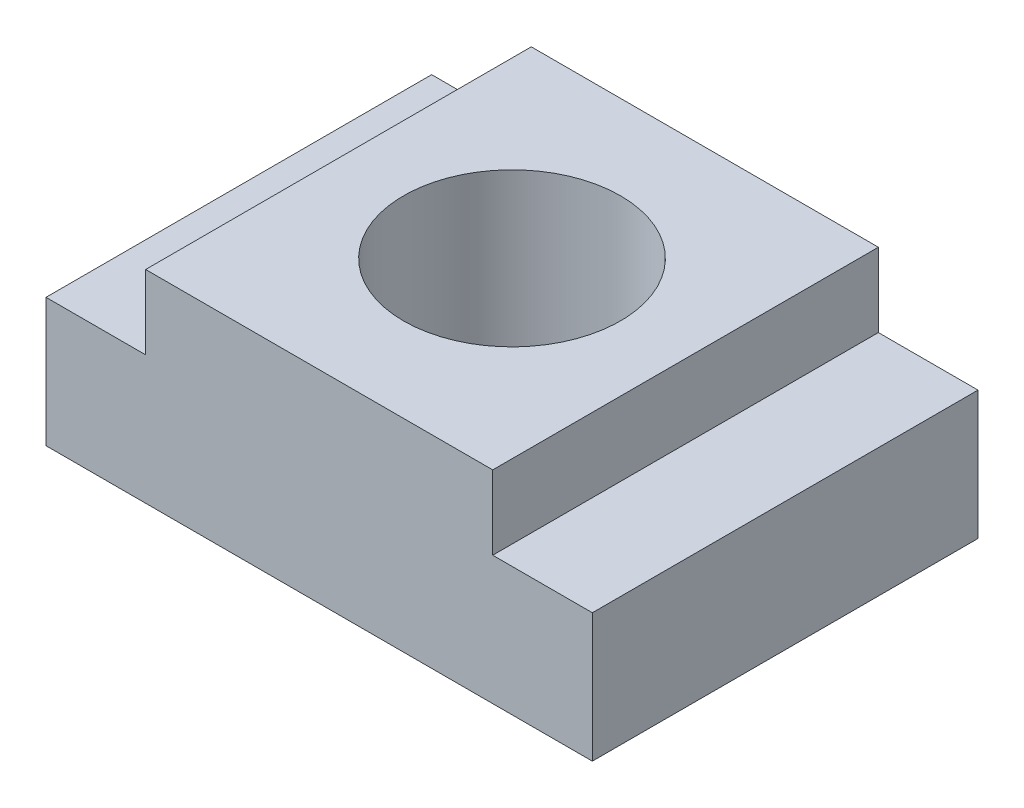
SolidWorks part; units mm, degrees
material "Chrome Stainless Steel"
ref_plane "Front Plane" through (0, 0, 0) normal (0, 0, 1) x (1, 0, 0)
ref_plane "Top Plane" through (0, 0, 0) normal (0, 1, 0) x (1, 0, 0)
ref_plane "Right Plane" through (0, 0, 0) normal (1, 0, 0) x (0, 0, -1)
sketch "Sketch1" plane through (0, 0, 0) normal (0, 0, 1) x (1, 0, 0)
  line L0 (0, 6.3) -> (5.4, 6.3)
  line L1 (0, -55) -> (0, 55) construction
  line L2 (5.4, 6.3) -> (5.4, 4)
  line L3 (5.4, 4) -> (8.5, 4)
  line L4 (8.5, 4) -> (8.5, 0)
  line L5 (55, 0) -> (-55, 0) construction
  line L6 (8.5, 0) -> (0, 0)
  line L7 (0, 0) -> (0, 6.3)
  dimension "D1" = 5.4
  dimension "D2" = 2.3
  dimension "D3" = 4
  dimension "D4" = 8.5
extrude "Boss-Extrude1" add sketch "Sketch1" along normal blind 12
mirror "Mirror1" about plane through (0, 0, 0) normal (1, 0, 0) of "Boss-Extrude1"
sketch "Sketch2" plane through (0, 6.3, 0) normal (0, 1, 0) x (1, 0, 0)
  line L0 (0, -3.465) -> (0, 3.465) construction
  line L1 (-3.465, 0) -> (3.465, 0) construction
  circle A0 centre (0, -6) radius 3.375
  dimension "D1" = 6.75
  dimension "D2" = 6
extrude "Cut-Extrude1" cut sketch "Sketch2" against normal blind 7
fillet "Fillet1" [suppressed] radius 0.1
